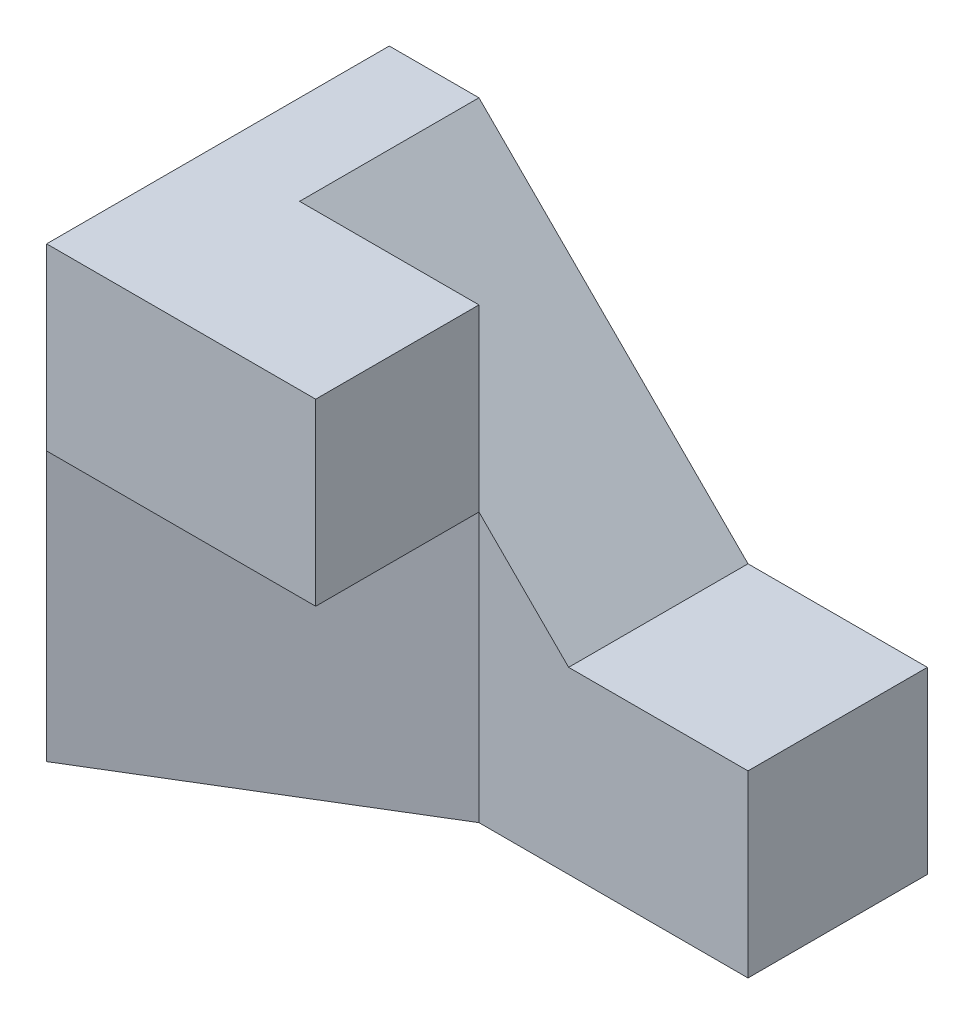
SolidWorks part; units mm, degrees
ref_plane "Front Plane" through (0, 0, 0) normal (0, 0, 1) x (1, 0, 0)
ref_plane "Top Plane" through (0, 0, 0) normal (0, 1, 0) x (1, 0, 0)
ref_plane "Right Plane" through (0, 0, 0) normal (1, 0, 0) x (0, 0, -1)
sketch "Sketch1" plane through (0, 0, 0) normal (0, 0, 1) x (1, 0, 0)
  line L0 (0, 0) -> (6, 0)
  line L1 (6, 0) -> (6, 2)
  line L2 (6, 2) -> (4, 2)
  line L3 (4, 2) -> (1, 5)
  line L4 (1, 5) -> (0, 5)
  line L5 (0, 5) -> (0, 0)
  dimension "D1" = 5
  dimension "D2" = 6
  dimension "D3" = 2
  dimension "D4" = 2
  dimension "D5" = 1
extrude "Boss-Extrude1" add sketch "Sketch1" against normal blind 2
sketch "Sketch2" plane through (0, 0, 0) normal (-1, 0, 0) x (0, 0, 1)
  line L1 (0, 5) -> (1.8206, 5)
  line L2 (0, 5) -> (0, 3)
  line L3 (0, 3) -> (1.8206, 3)
  line L4 (1.8206, 5) -> (1.8206, 3)
  dimension "D1" = 2
extrude "Boss-Extrude2" add sketch "Sketch2" against normal blind 3 separate body
sketch "Sketch3" plane through (0, 3, 0) normal (0, -1, 0) x (1, 0, 0)
  line L0 (0, 0) -> (3, 0)
  line L2 (3, 0) -> (0, 1.8206)
  line L3 (0, 0) -> (0, 1.8206)
extrude "Boss-Extrude3" add sketch "Sketch3" along normal blind 3
